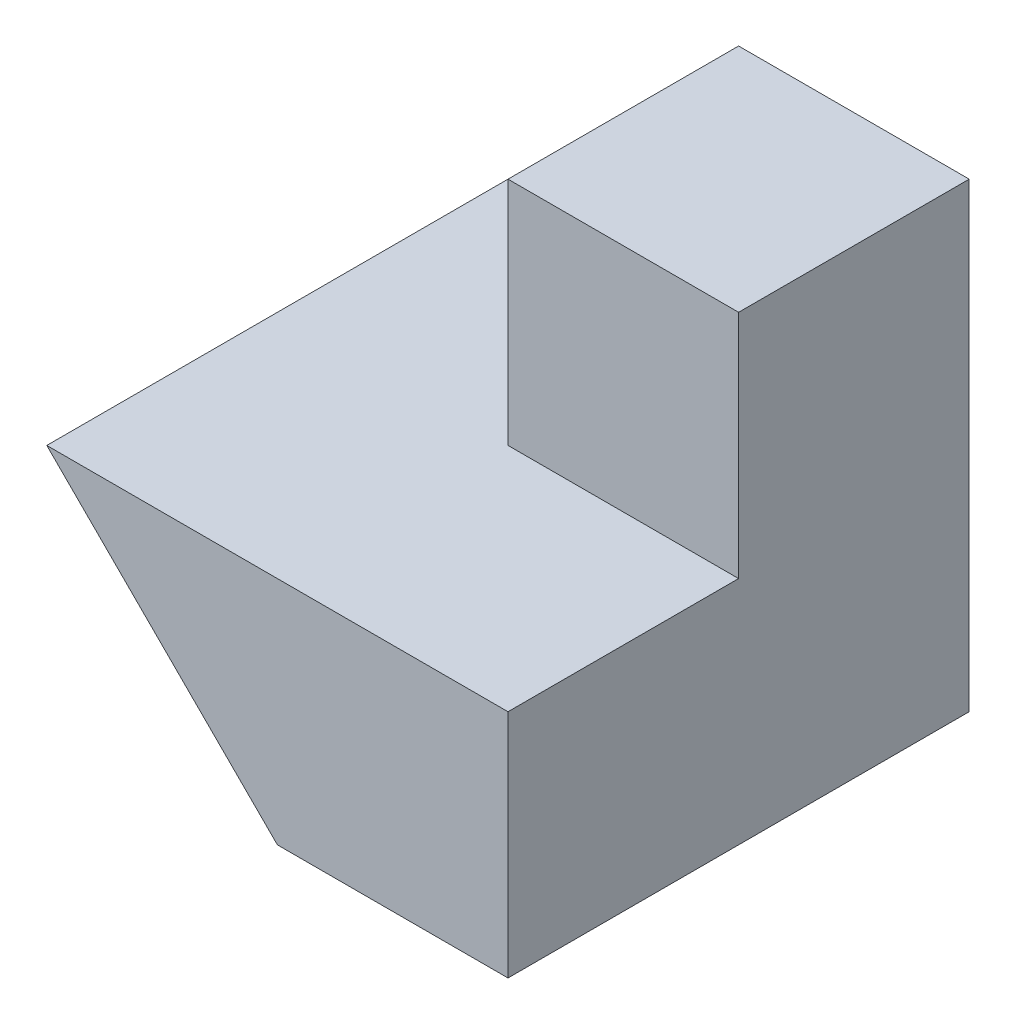
SolidWorks part; units mm, degrees
ref_plane "Front Plane" through (0, 0, 0) normal (0, 0, 1) x (1, 0, 0)
ref_plane "Top Plane" through (0, 0, 0) normal (0, 1, 0) x (1, 0, 0)
ref_plane "Right Plane" through (0, 0, 0) normal (1, 0, 0) x (0, 0, -1)
sketch "Sketch1" plane through (0, 0, 0) normal (0, 0, 1) x (1, 0, 0)
  line L1 (0, 0) -> (40, 0)
  line L2 (0, 0) -> (0, 40)
  line L3 (0, 40) -> (40, 40)
  line L4 (40, 0) -> (40, 40)
  dimension "D1" = 40
  dimension "D2" = 40
extrude "Boss-Extrude1" add sketch "Sketch1" along normal blind 40
sketch "Sketch2" plane through (0, 0, 40) normal (0, 0, 1) x (1, 0, 0)
  line L1 (0, 40) -> (20, 40)
  line L2 (0, 40) -> (0, 20)
  line L3 (0, 20) -> (20, 20)
  line L4 (20, 40) -> (20, 20)
  dimension "D1" = 20
  dimension "D2" = 20
extrude "Cut-Extrude1" cut sketch "Sketch2" against normal blind 40
sketch "Sketch3" plane through (20, 0, 0) normal (-1, 0, 0) x (0, 0, 1)
  line L0 (0, 20) -> (40, 20) construction
  line L1 (40, 40) -> (20, 40)
  line L2 (40, 40) -> (40, 20)
  line L3 (40, 20) -> (20, 20)
  line L4 (20, 40) -> (20, 20)
extrude "Cut-Extrude2" cut sketch "Sketch3" against normal blind 40
sketch "Sketch4" plane through (0, 0, 40) normal (0, 0, 1) x (1, 0, 0)
  line L0 (0, 20) -> (20, 0)
  line L1 (0, 0) -> (40, 0) construction
  line L2 (20, 0) -> (0, 0)
  line L3 (0, 0) -> (0, 20)
extrude "Cut-Extrude3" cut sketch "Sketch4" against normal blind 20
